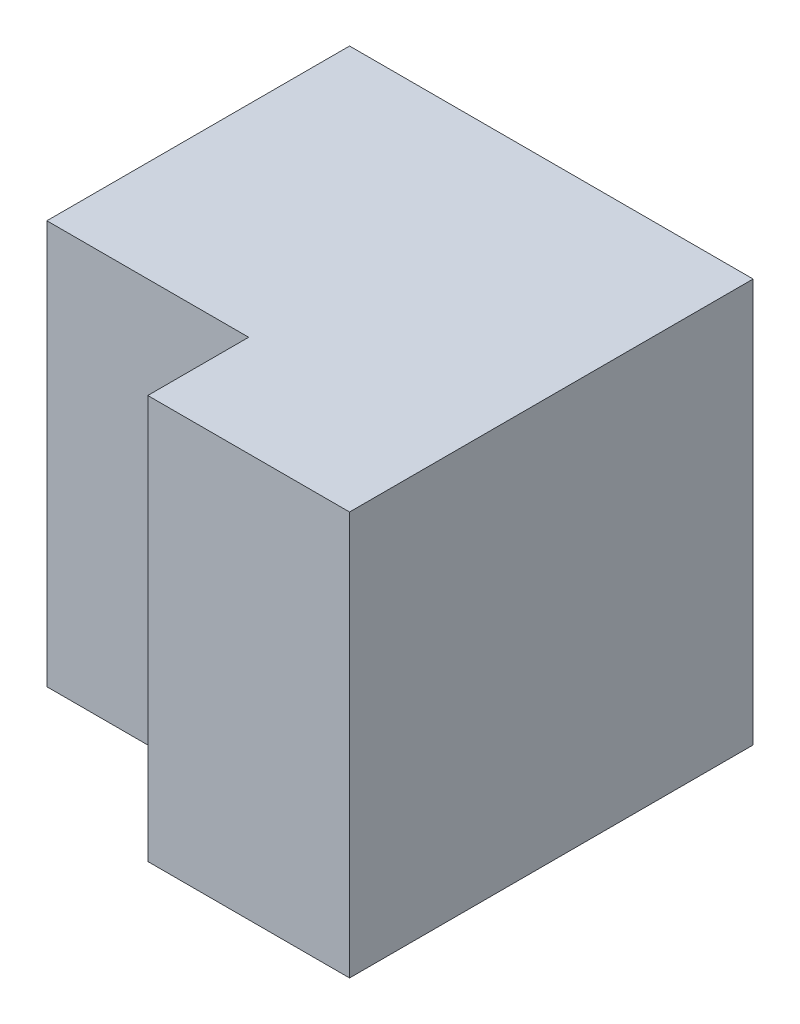
SolidWorks part; units mm, degrees
ref_plane "Front Plane" through (0, 0, 0) normal (0, 0, 1) x (1, 0, 0)
ref_plane "Top Plane" through (0, 0, 0) normal (0, 1, 0) x (1, 0, 0)
ref_plane "Right Plane" through (0, 0, 0) normal (1, 0, 0) x (0, 0, -1)
sketch "Sketch1" plane through (0, 0, 0) normal (1, 0, 0) x (0, 0, -1)
  line L1 (0, 0) -> (4, 0)
  line L2 (0, 0) -> (0, 4)
  line L3 (0, 4) -> (4, 4)
  line L4 (4, 0) -> (4, 4)
  dimension "D1" = 4
  dimension "D2" = 4
extrude "Boss-Extrude1" add sketch "Sketch1" along normal blind 2
sketch "Sketch2" plane through (0, 0, 0) normal (-1, 0, 0) x (0, 0, 1)
  line L0 (-1, 0) -> (-1, 4)
  line L1 (0, 0) -> (-4, 0) construction
  line L2 (-4, 0) -> (-4, 4) construction
  line L3 (-4, 4) -> (-4, 0)
  line L4 (-4, 0) -> (-1, 0)
  line L5 (-4, 4) -> (0, 4) construction
  line L6 (-1, 4) -> (-4, 4)
  dimension "D1" = 3
  dimension "D2" = 4
extrude "Boss-Extrude2" add sketch "Sketch2" along normal blind 2
